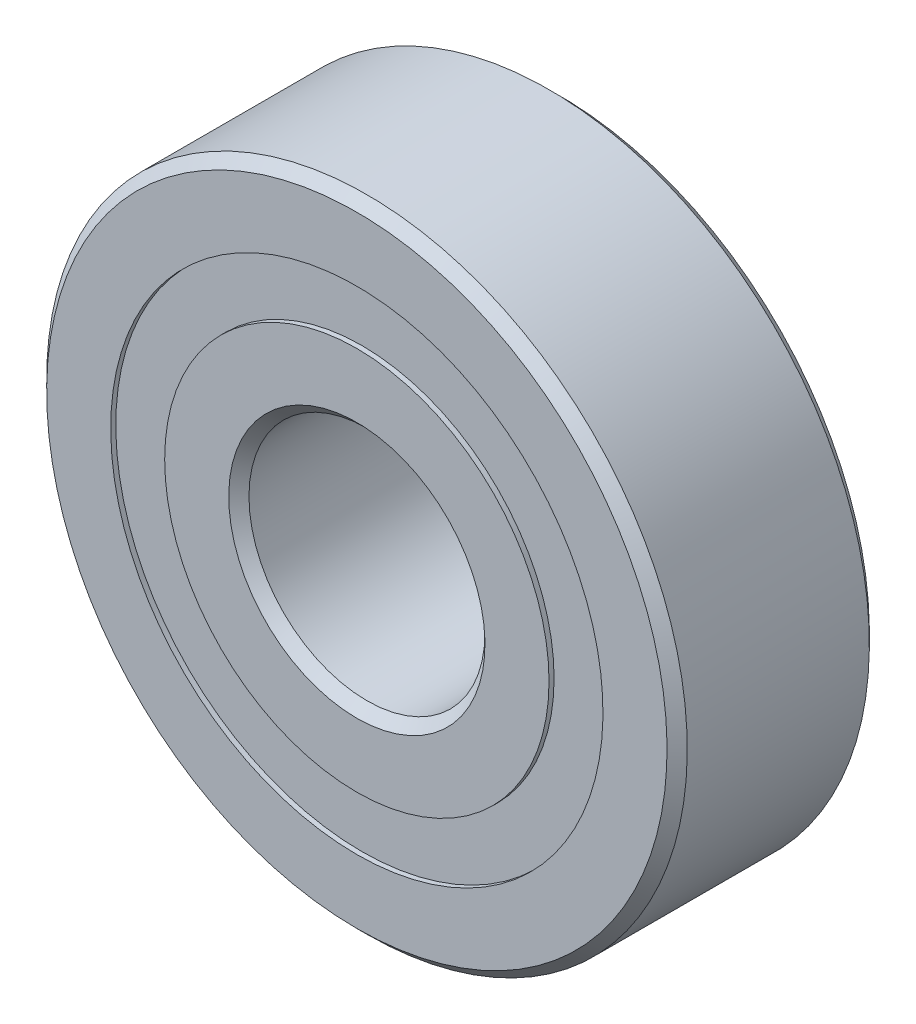
SolidWorks part; units mm, degrees
ref_plane "Front Plane" through (0, 0, 0) normal (0, 0, 1) x (1, 0, 0)
ref_plane "Top Plane" through (0, 0, 0) normal (0, 1, 0) x (1, 0, 0)
ref_plane "Right Plane" through (0, 0, 0) normal (1, 0, 0) x (0, 0, -1)
sketch "Sketch1" plane through (0, 0, 0) normal (0, 0, 1) x (1, 0, 0)
  line L0 (-9.5, 0) -> (9.5, 0) construction
  line L1 (-3.5, 0) -> (3.5, 0) construction
  circle A0 centre (0, 0) radius 3.5 construction
  circle A1 centre (0, 0) radius 9.5 construction
  point P3 (0, 0)
  point P6 (0, 0)
  point P7 (0, -3.5)
  point P11 (0, -9.5)
  point P12 (0, 3.5)
  point P13 (0, 9.5)
  dimension "OD" = 19
  dimension "ID" = 7
sketch "SketchB" plane through (0, 0, 0) normal (1, 0, 0) x (0, 0, -1)
  line L0 (-3, 9.5) -> (3, 9.5) construction
  line L1 (0, 9.5) -> (0, -9.5) construction
  line L2 (2.7, 9.5) -> (-2.7, 9.5)
  line L3 (-2.7, 9.5) -> (-3, 9.2)
  line L4 (-3, 9.2) -> (-3, 7.3)
  line L5 (-3, 7.3) -> (-1.3333, 7.3)
  line L6 (3, 7.3) -> (1.3333, 7.3)
  line L7 (3, 9.2) -> (3, 7.3)
  line L8 (2.7, 9.5) -> (3, 9.2)
  line L9 (0, 9.5) -> (0, 6.5) construction
  line L10 (0, 6.5) -> (0, 3.5) construction
  line L11 (0, 9.5) -> (0, -9.5) construction
  line L12 (-3, 0) -> (3, 0) construction
  line L13 (3, 3.5) -> (-3, 3.5) construction
  line L15 (-3, -3.5) -> (3, -3.5) construction
  arc A0 (-1.3333, 7.3) -> (1.3333, 7.3) centre (0, 6.5) cw
  circle A1 centre (0, 6.5) radius 1.5549 construction
  point P14 (0, 3.5)
  point P17 (0, 0)
  point P21 (0, 9.5)
  point P29 (0, 3.5)
  point P30 (0, -3.5)
  dimension "Width" = 6
  dimension "D1" = 45
  dimension "D2" = 0.3
  dimension "D3" = 2.6667
  dimension "D4" = 0.8
sketch "Sketch7" plane through (0, 0, 0) normal (1, 0, 0) x (0, 0, -1)
  line L0 (2.7, 9.5) -> (3, 9.2) construction
  line L1 (3, 9.2) -> (3, 7.3) construction
  line L2 (3, 7.3) -> (1.3333, 7.3) construction
  line L3 (-3, 7.3) -> (-1.3333, 7.3) construction
  line L4 (-3, 9.2) -> (-3, 7.3) construction
  line L5 (-2.7, 9.5) -> (-3, 9.2) construction
  line L6 (2.7, 9.5) -> (-2.7, 9.5) construction
  line L7 (2.7, 9.5) -> (3, 9.2)
  line L8 (3, 9.2) -> (3, 7.3)
  line L9 (3, 7.3) -> (1.3333, 7.3)
  line L10 (-3, 7.3) -> (-1.3333, 7.3)
  line L11 (-3, 9.2) -> (-3, 7.3)
  line L12 (-2.7, 9.5) -> (-3, 9.2)
  line L13 (2.7, 9.5) -> (-2.7, 9.5)
  arc A0 (1.3333, 7.3) -> (-1.3333, 7.3) centre (0, 6.5) ccw construction
  arc A1 (1.3333, 7.3) -> (-1.3333, 7.3) centre (0, 6.5) ccw
revolve "Revolve6" add sketch "Sketch7" angle 360 about L12
sketch "Sketch3" plane through (0, 0, 0) normal (1, 0, 0) x (0, 0, -1)
  line L0 (0, 9.5) -> (0, -9.5) construction
  line L1 (0, 9.5) -> (0, -9.5) construction
  line L2 (-2.7, 3.5) -> (-3, 3.8)
  line L3 (-3, 3.8) -> (-3, 5.7)
  line L5 (-3, 5.7) -> (-1.3333, 5.7)
  line L6 (-2.7, 3.5) -> (2.7, 3.5)
  line L8 (2.7, 3.5) -> (3, 3.8)
  line L10 (3, 3.8) -> (3, 5.7)
  line L11 (3, 5.7) -> (1.3333, 5.7)
  line L12 (-3, 9.2) -> (-3, 7.3) construction
  line L13 (2.7, 9.5) -> (3, 9.2) construction
  line L15 (3, -9.2) -> (3, 9.2) construction
  line L16 (2.7, 9.5) -> (2.7, -9.5) construction
  arc A1 (1.3333, 5.7) -> (-1.3333, 5.7) centre (0, 6.5) cw
  circle A2 centre (0, 6.5) radius 1.5549 construction
  point P1 (0, 3.5)
revolve "Revolve3" add sketch "Sketch3" angle 360 about L12
sketch "Sketch4" plane through (0, 0, 0) normal (1, 0, 0) x (0, 0, -1)
  line L0 (-1.5549, 6.5) -> (1.5549, 6.5)
  arc A2 (-1.5549, 6.5) -> (1.5549, 6.5) centre (0, 6.5) cw
  arc A3 (1.3333, 7.3) -> (-1.3333, 7.3) centre (0, 6.5) ccw construction
revolve "Revolve4" add sketch "Sketch4" angle 360 about L0
pattern_circular "CirPattern1" count 6 over 360 about axis through (0, 0, 0) along (0, 0, 1) of bodies 104
sketch "Sketch5" plane through (0, 0, 0) normal (1, 0, 0) x (0, 0, -1)
  line L0 (-3, 7.3) -> (-1.3333, 7.3) construction
  line L1 (-2.85, 7.3) -> (-1.5549, 7.3)
  line L2 (-2.85, 7.3) -> (-2.85, 5.7)
  line L3 (-2.85, 5.7) -> (-1.5549, 5.7)
  line L4 (-1.5549, 7.3) -> (-1.5549, 5.7)
  line L5 (-3, 5.7) -> (-1.3333, 5.7) construction
  line L6 (-2.7, 9.5) -> (-3, 9.2) construction
  line L7 (0, 9.5) -> (0, 3.5) construction
  line L8 (2.85, 5.7) -> (1.5549, 5.7)
  line L9 (1.5549, 7.3) -> (1.5549, 5.7)
  line L10 (2.85, 7.3) -> (1.5549, 7.3)
  line L11 (2.85, 7.3) -> (2.85, 5.7)
  circle A1 centre (0, 6.5) radius 1.5549 construction
  point P10 (-2.85, 9.35)
revolve "Revolve5" add sketch "Sketch5" angle 360 about L12
equation "\"D2@SketchB\" = \"Width@SketchB\" * .05"
equation "\"D3@SketchB\" = \"Width@SketchB\" / 2.25"
equation "\"D4@SketchB\" =  (  (  ( \"OD@Sketch1\" - \"Width@SketchB\" )  / 2 )  / 3.25 )  / 2.5"
